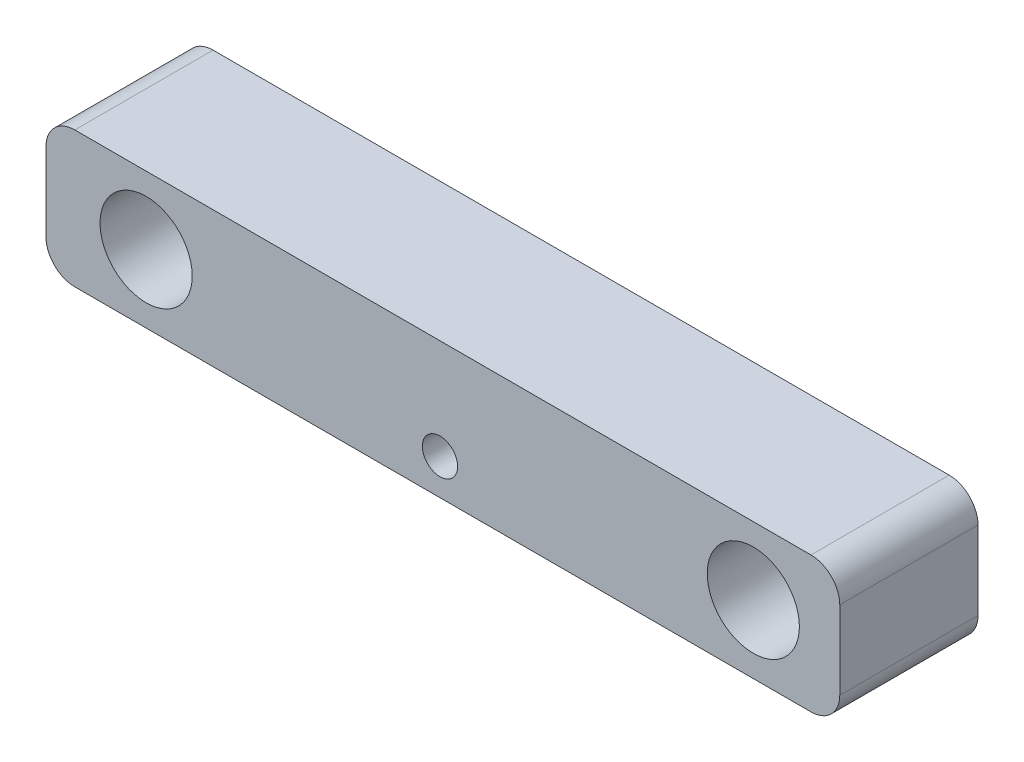
SolidWorks part; units mm, degrees
ref_plane "Front Plane" through (0, 0, 0) normal (0, 0, 1) x (1, 0, 0)
ref_plane "Top Plane" through (0, 0, 0) normal (0, 1, 0) x (1, 0, 0)
ref_plane "Right Plane" through (0, 0, 0) normal (1, 0, 0) x (0, 0, -1)
sketch "Sketch5" plane through (0, 0, 0) normal (0, 0, 1) x (1, 0, 0)
  line L1 (-159.6602, 19.6532) -> (15.3458, 19.6532)
  line L2 (-159.6602, 19.6532) -> (-159.6602, -10.3188)
  line L3 (-159.6602, -10.3188) -> (15.3458, -10.3188)
  line L4 (15.3458, 19.6532) -> (15.3458, -10.3188)
  line L5 (-159.6602, 19.6532) -> (15.3458, -10.3188) construction
  line L6 (-159.6602, -10.3188) -> (15.3458, 19.6532) construction
  circle A0 centre (-137.5833, 4.6672) radius 10.16
  circle A1 centre (-3.7156, 4.6672) radius 10.16
  point P0 (-72.1572, 4.6672)
  dimension "D1" = 175.006
  dimension "D2" = 29.972
extrude "Boss-Extrude11" add sketch "Sketch5" along normal blind 30.48
sketch "Sketch7" plane through (0, 0, 30.48) normal (0, 0, 1) x (1, 0, 0)
  line L5 (-75.043, 0.7465) -> (-70.543, -5.5935) construction
  line L6 (-75.043, -5.5935) -> (-70.543, 0.7465) construction
  circle A0 centre (-72.793, -2.4235) radius 3.8873
  point P0 (-72.793, -2.4235)
  dimension "D1" = 6.34
  dimension "D2" = 4.5
sketch "Sketch12" plane through (0, 0, 30.48) normal (0, 0, 1) x (1, 0, 0)
  line L0 (-72.9182, 19.6532) -> (-72.9182, -10.3188) construction
  line L1 (15.3458, 19.6532) -> (-159.6602, 19.6532) construction
  line L2 (-159.6602, -10.3188) -> (15.3458, -10.3188) construction
sketch "Sketch14" plane through (0, 0, 30.48) normal (0, 0, 1) x (1, 0, 0)
extrude "Cut-Extrude6" cut sketch "Sketch7" against normal blind 7.62
fillet "Fillet1" radius 6.35 4 edges at (15.3458, 19.6532, 15.24) (15.3458, -10.3188, 15.24) (-159.6602, -10.3188, 15.24) (-159.6602, 19.6532, 15.24)
